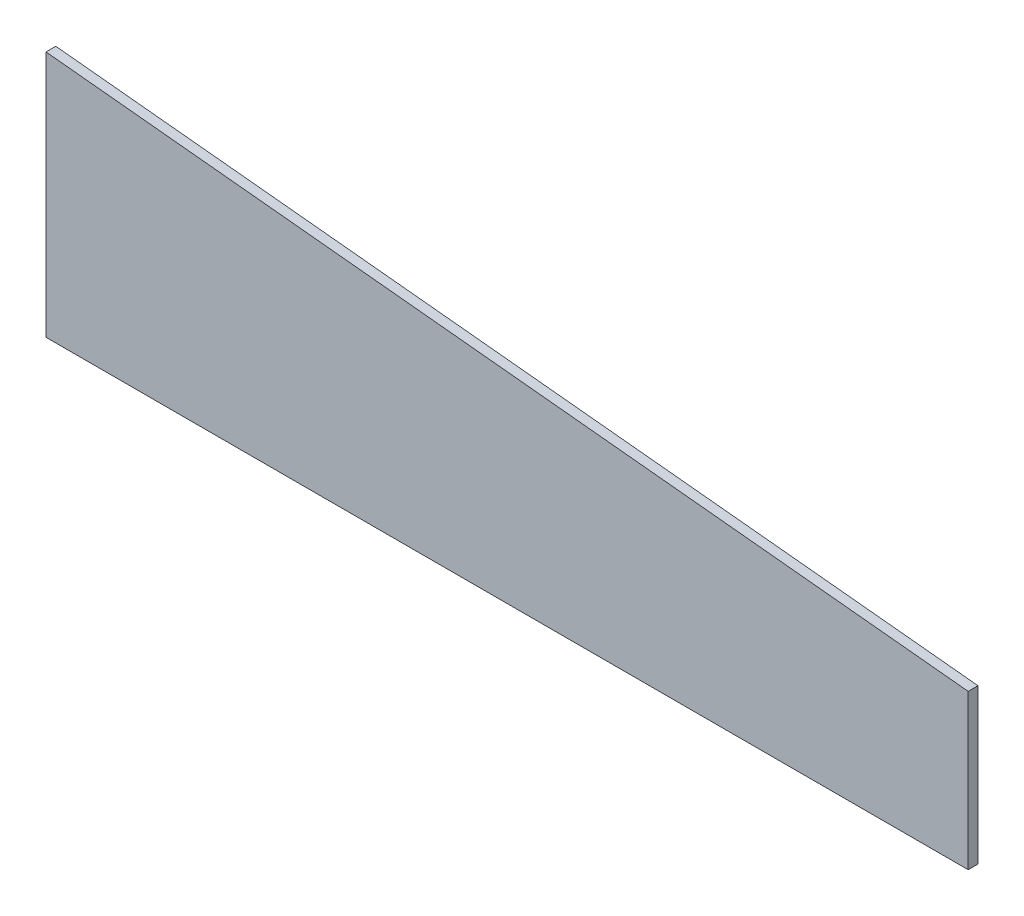
SolidWorks part; units mm, degrees
ref_plane "Plan de face" through (0, 0, 0) normal (0, 0, 1) x (1, 0, 0)
ref_plane "Plan de dessus" through (0, 0, 0) normal (0, 1, 0) x (1, 0, 0)
ref_plane "Plan de droite" through (0, 0, 0) normal (1, 0, 0) x (0, 0, -1)
sketch "Esquisse1" plane through (0, 0, 0) normal (0, 0, 1) x (1, 0, 0)
  line L0 (-149.2481, 40) -> (-149.2481, 0)
  line L1 (-149.2481, 0) -> (0, 0)
  line L2 (0, 0) -> (0, 25)
  line L3 (0, 25) -> (-149.2481, 40)
  dimension "D1" = 25
  dimension "D2" = 40
  dimension "D3" = 150
extrude "Boss.-Extru.1" add sketch "Esquisse1" along normal blind 1.5875
